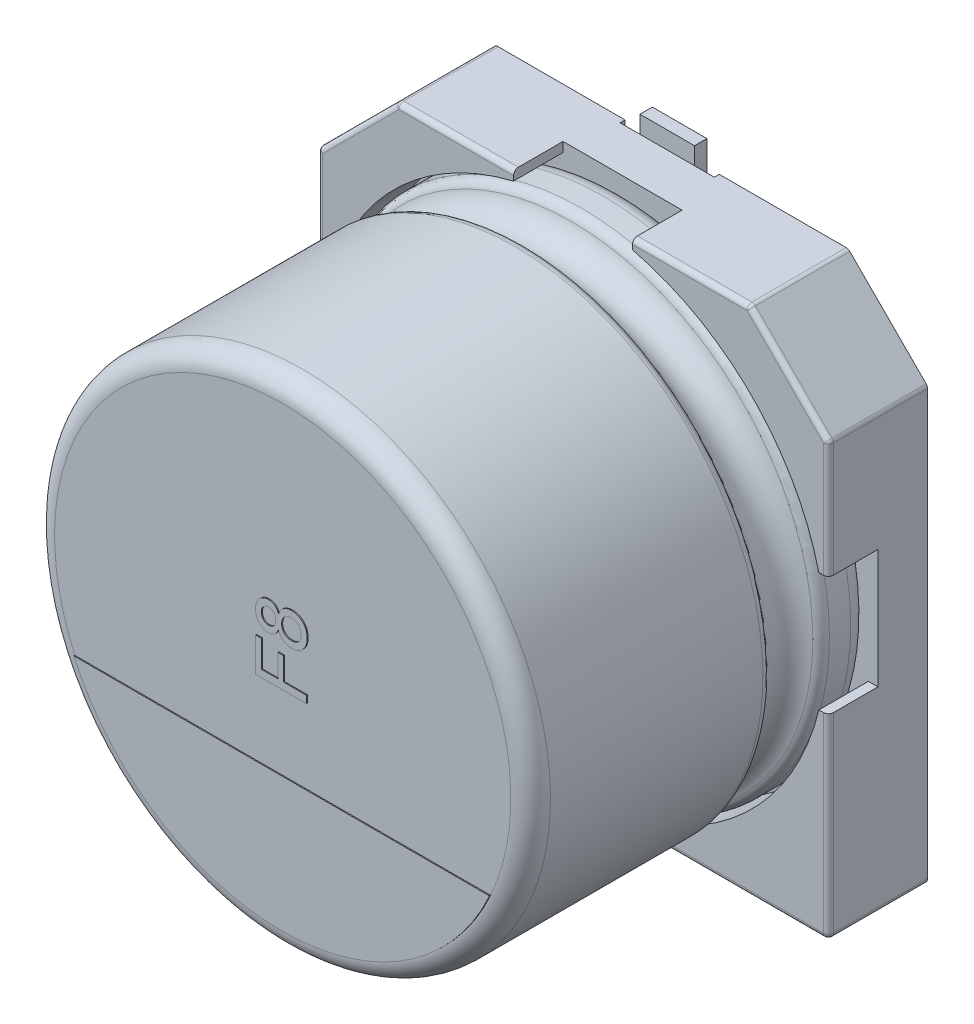
SolidWorks part; units mm, degrees
ref_plane "Plan de face" through (0, 0, 0) normal (0, 0, 1) x (1, 0, 0)
ref_plane "Plan de dessus" through (0, 0, 0) normal (0, 1, 0) x (1, 0, 0)
ref_plane "Plan de droite" through (0, 0, 0) normal (1, 0, 0) x (0, 0, -1)
sketch "Sketch2" plane through (0, 0, 0) normal (0, 0, 1) x (1, 0, 0)
  line L0 (-5.15, 3.55) -> (-3.55, 5.15)
  line L1 (-3.55, 5.15) -> (3.55, 5.15)
  line L2 (-5.15, 3.55) -> (-5.15, -5.15)
  line L3 (-5.15, -5.15) -> (5.15, -5.15)
  line L4 (5.15, 3.55) -> (5.15, -5.15)
  line L5 (-5.15, 5.15) -> (5.15, -5.15) construction
  line L6 (-5.15, -5.15) -> (5.15, 5.15) construction
  line L7 (3.55, 5.15) -> (5.15, 3.55)
  point P0 (0, 0)
  dimension "D1" = 10.3
  dimension "D2" = 10.3
extrude "Boss-Extrude1" add sketch "Sketch2" along normal blind 1
sketch "Sketch4" plane through (0, 0, 1) normal (0, 0, 1) x (1, 0, 0)
  line L0 (-5.15, 3.55) -> (-3.55, 5.15)
  line L1 (-3.55, 5.15) -> (-1.2, 5.15)
  line L3 (-5.15, 1.2) -> (-5.15, 3.55)
  line L4 (3.55, 5.15) -> (5.15, 3.55)
  line L5 (5.15, 3.55) -> (5.15, 1.2)
  line L6 (5.15, -5.15) -> (5.15, 3.55) construction
  line L7 (3.55, 5.15) -> (-3.55, 5.15) construction
  line L8 (1.2, 5.15) -> (3.55, 5.15)
  line L9 (-5.15, -5.15) -> (5.15, -5.15) construction
  line L10 (5.15, -1.2) -> (5.15, -5.15)
  line L11 (5.15, -5.15) -> (1.2, -5.15)
  line L12 (-5.15, -1.2) -> (-5.15, -5.15)
  line L13 (-5.15, -5.15) -> (-1.2, -5.15)
  line L14 (-4.946, -1.2) -> (4.946, -1.2) construction
  line L15 (-4.8253, 1.2) -> (5.0249, 1.2) construction
  line L16 (4.9568, 1.2) -> (5.15, 1.2)
  line L17 (4.9568, -1.2) -> (5.15, -1.2)
  line L18 (-4.9568, -1.2) -> (-5.15, -1.2)
  line L19 (-4.9568, 1.2) -> (-5.15, 1.2)
  line L20 (-1.2, 5.0139) -> (-1.2, -5.2906) construction
  line L21 (1.2, 5.0139) -> (1.2, -5.4) construction
  line L22 (-1.2, 5.15) -> (-1.2, 4.9568)
  line L23 (1.2, 5.15) -> (1.2, 4.9568)
  line L24 (-1.2, -4.9568) -> (-1.2, -5.15)
  line L25 (1.2, -4.9568) -> (1.2, -5.15)
  arc A0 (-1.2, 4.9568) -> (-4.9568, 1.2) centre (0, 0) ccw construction
  arc A1 (-4.9568, 1.2) -> (-1.2, 4.9568) centre (0, 0) cw
  arc A2 (1.2, 4.9568) -> (4.9568, 1.2) centre (0, 0) cw
  arc A3 (1.2, -4.9568) -> (4.9568, -1.2) centre (0, 0) ccw
  arc A4 (-1.2, -4.9568) -> (-4.9568, -1.2) centre (0, 0) cw
  arc A5 (4.9568, 1.2) -> (1.2, 4.9568) centre (0, 0) ccw construction
  arc A6 (1.2, -4.9568) -> (4.9568, -1.2) centre (0, 0) ccw construction
  arc A7 (-4.9568, -1.2) -> (-1.2, -4.9568) centre (0, 0) ccw construction
  point P33 (0, -1.2)
  dimension "D1" = 10.2
  dimension "D2" = 1.2
  dimension "D3" = 1.2
  dimension "D4" = 1.2
  dimension "D5" = 1.2
sketch "Sketch5" plane through (0, 0, 0) normal (0, 0, 1) x (1, 0, 0)
extrude "Boss-Extrude2" add sketch "Sketch4" along normal blind 1
sketch "Sketch7" plane through (0, 0, 0) normal (0, 0, -1) x (1, 0, 0)
  line L1 (-3.5816, 3.5474) -> (3.5816, 3.5474) construction
  line L2 (-3.5816, 3.5474) -> (-3.5816, -3.5474) construction
  line L3 (-3.5816, -3.5474) -> (3.5816, -3.5474) construction
  line L4 (3.5816, 3.5474) -> (3.5816, -3.5474) construction
  line L5 (-3.5816, 3.5474) -> (3.5816, -3.5474) construction
  line L6 (-3.5816, -3.5474) -> (3.5816, 3.5474) construction
  circle A0 centre (-3.5816, 3.5474) radius 0.35
  circle A1 centre (3.5816, 3.5474) radius 0.35
  circle A2 centre (-3.5816, -3.5474) radius 0.35
  circle A3 centre (3.5816, -3.5474) radius 0.35
  point P0 (0, 0)
  point P10 (2.9065, 2.8449)
  point P11 (3.5816, 3.5474)
  dimension "D1" = 0.7
  dimension "D2" = 0.7
  dimension "D3" = 0.7
  dimension "D4" = 0.7
extrude "Spacer Pad" add sketch "Sketch7" along normal blind 0.15
sketch "Sketch8" plane through (0, 0, 0) normal (0, 0, -1) x (1, 0, 0)
  line L0 (-0.95, 4.3618) -> (-0.95, -4.4479) construction
  line L1 (0.95, 4.3618) -> (0.95, -4.4479) construction
  dimension "D1" = 0.95
  dimension "D2" = 1.9
sketch "Sketch9" plane through (0, 0, 0) normal (0, 0, -1) x (1, 0, 0)
  line L0 (-4.6239, -2.1) -> (5.0007, -2.1) construction
  line L1 (-4.6239, 2.1) -> (5.2975, 2.1) construction
  line L2 (-0.95, 4.3618) -> (-0.95, -4.4479) construction
  line L3 (-0.95, 2.1) -> (0.95, 2.1)
  line L4 (-0.95, 2.1) -> (-0.95, 5.15)
  line L5 (-0.95, 5.15) -> (0.95, 5.15)
  line L6 (0.95, 2.1) -> (0.95, 5.15)
  line L7 (0.95, 4.3618) -> (0.95, -4.4479) construction
  line L8 (-5.15, 5.15) -> (5.15, 5.15) construction
  line L9 (3.55, -5.15) -> (-3.55, -5.15) construction
  line L10 (-0.95, -2.1) -> (0.95, -2.1)
  line L11 (-0.95, -2.1) -> (-0.95, -5.15)
  line L12 (-0.95, -5.15) -> (0.95, -5.15)
  line L13 (0.95, -2.1) -> (0.95, -5.15)
  dimension "D1" = 2.1
  dimension "D2" = 2.1
extrude "Cut-Extrude1" cut sketch "Sketch9" against normal blind 0.1
fillet "Fillet1" radius 0.1 6 edges at (-5.15, 3.55, 1) (-3.55, 5.15, 1) (3.55, 5.15, 1) (5.15, 3.55, 1) (5.15, -5.15, 1) (-5.15, -5.15, 1)
sketch "Sketch10" plane through (0, 0, 0) normal (1, 0, 0) x (0, 0, -1)
  line L0 (18.9631, 0) -> (-18.9631, 0) construction
  line L2 (-7.8536, 0) -> (-7.8536, 4.6)
  line L3 (-7.4536, 5) -> (-3.1708, 5)
  line L4 (-1, 4.6) -> (-1, 0)
  line L7 (-1.8292, 5) -> (-1.4, 5)
  arc A0 (-7.8536, 4.6) -> (-7.4536, 5) centre (-7.4536, 4.6) cw
  arc A1 (-1.4, 5) -> (-1, 4.6) centre (-1.4, 4.6) cw
  arc A2 (-2.9792, 4.8571) -> (-2.0208, 4.8571) centre (-2.5, 5) ccw
  arc A3 (-3.1708, 5) -> (-2.9792, 4.8571) centre (-3.1708, 4.8) cw
  arc A4 (-2.0208, 4.8571) -> (-1.8292, 5) centre (-1.8292, 4.8) cw
  point P4 (0, 1)
  point P13 (-7.8536, 5)
  dimension "D2" = 0.4
  dimension "D3" = 0.4
  dimension "D4" = 0.2
  dimension "D1" = 5
revolve "Revolve1" add sketch "Sketch10" angle 360 about L0
fillet "Fillet2" radius 0.1 16 edges at (3.125, -5.15, 2) (5.1207, -5.1207, 2) (5.15, 2.3543, 2) (5.1424, 3.5468, 2) (2.3543, 5.15, 2) (3.5468, 5.1424, 2) (-2.3543, 5.15, 2) (-3.5468, 5.1424, 2) (-4.35, 4.35, 2) (-5.1424, 3.5468, 2) (-5.15, -3.125, 2) (-5.1207, -5.1207, 2) (5.15, -3.125, 2) (4.35, 4.35, 2) (-5.15, 2.3543, 2) (-3.125, -5.15, 2)
sketch "Sketch13" plane through (0, 0, 7.8536) normal (0, 0, 1) x (1, 0, 0)
  line L0 (-6.1745, -1.8934) -> (2.8059, -1.8934) construction
  line L1 (-4.1923, -1.8934) -> (4.1923, -1.8934)
  arc A0 (4.1923, -1.8934) -> (-4.1923, -1.8934) centre (0, 0) cw
  point P3 (-1.6843, -1.8934)
extrude "Cathode marker" add sketch "Sketch13" along normal blind 0.02
sketch "Sketch15" plane through (0, 0, 7.8536) normal (0, 0, 1) x (1, 0, 0)
  line L1 (0.5, 2.1812) -> (0.5, -0.5) construction
  text T1 "F8" font "Arial" height in points 4
extrude "Text" add sketch "Sketch15" along normal blind 0.02
sketch "Sketch18" plane through (0, 0, 0.1) normal (0, 0, -1) x (1, 0, 0)
  line L0 (0, 5.1012) -> (0, -5.1012) construction
  point P4 (0, 0)
sketch "Sketch19" plane through (0, 0, 0.1) normal (0, 0, -1) x (1, 0, 0)
  line L0 (-1.0534, -5.5) -> (1.0534, -5.5) construction
  line L2 (-0.95, -5.15) -> (0.95, -5.15) construction
  line L3 (-1.9391, 5.5) -> (1.9391, 5.5) construction
  line L5 (0.95, 5.15) -> (-0.95, 5.15) construction
  line L6 (0, 5.1012) -> (0, -5.1012) construction
  line L7 (-0.55, 2.3) -> (0.55, 2.3)
  line L8 (-0.55, 2.3) -> (-0.55, 5.5)
  line L9 (-0.55, 5.5) -> (0.55, 5.5)
  line L10 (0.55, 2.3) -> (0.55, 5.5)
  line L11 (-0.55, 2.3) -> (0.55, 5.5) construction
  line L12 (-0.55, 5.5) -> (0.55, 2.3) construction
  line L14 (-0.55, -2.3) -> (0.55, -2.3)
  line L15 (-0.55, -2.3) -> (-0.55, -5.5)
  line L16 (-0.55, -5.5) -> (0.55, -5.5)
  line L17 (0.55, -2.3) -> (0.55, -5.5)
  line L18 (-0.55, -2.3) -> (0.55, -5.5) construction
  line L19 (-0.55, -5.5) -> (0.55, -2.3) construction
  point P3 (0, -5.5)
  point P8 (0, 5.5)
  point P10 (0, 3.9)
  point P17 (0, -3.9)
  dimension "D1" = 0.35
  dimension "D2" = 0.35
  dimension "D3" = 1.1
  dimension "D4" = 3.2
  dimension "D5" = 1.1
  dimension "D6" = 3.2
extrude "Boss-Extrude6" add sketch "Sketch19" along normal blind 0.25
